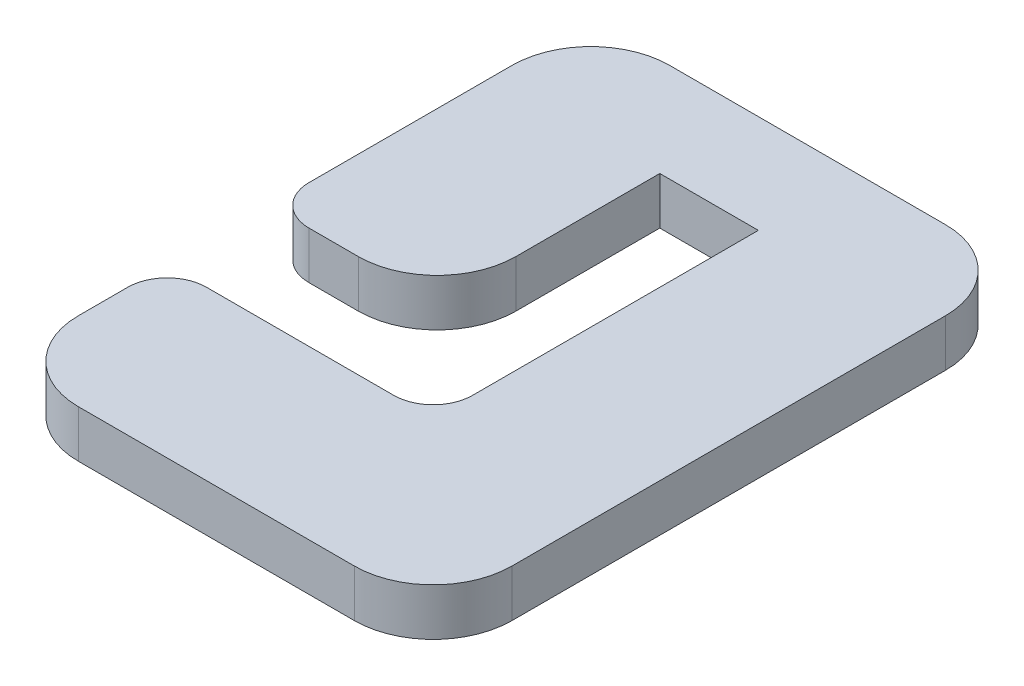
SolidWorks part; units mm, degrees
ref_plane "Front Plane" through (0, 0, 0) normal (0, 0, 1) x (1, 0, 0)
ref_plane "Top Plane" through (0, 0, 0) normal (0, 1, 0) x (1, 0, 0)
ref_plane "Right Plane" through (0, 0, 0) normal (1, 0, 0) x (0, 0, -1)
sketch "Sketch1" plane through (0, 0, 0) normal (0, 1, 0) x (1, 0, 0)
  line L0 (0, -6.5) -> (0, 0) construction
  line L1 (-11, -15) -> (11, -15)
  line L2 (-11, -15) -> (-11, -6.5)
  line L3 (-11, 15) -> (11, 15)
  line L4 (11, -15) -> (11, 15)
  line L5 (-11, -15) -> (-2.5, -3.4091) construction
  line L6 (-11, 15) -> (11, -15) construction
  line L7 (-2.5, 10) -> (2.5, 10)
  line L8 (-2.5, 10) -> (-2.5, -1.3)
  line L9 (-2.5, -6.5) -> (2.5, -6.5)
  line L10 (2.5, 10) -> (2.5, -6.5)
  line L11 (-2.5, -3.4091) -> (0, 0) construction
  line L12 (-2.5, -1.3) -> (-11, -1.3)
  line L13 (-2.5, -3.4091) -> (-2.5, -6.5) construction
  line L14 (-2.5, -6.5) -> (-11, -6.5)
  line L15 (-11, -1.3) -> (-11, -6.5) construction
  line L16 (0, 0) -> (11, 15) construction
  line L17 (-2.5, -1.3) -> (-2.5, -3.4091) construction
  line L18 (-2.5, -3.4091) -> (-2.5, -6.5) construction
  line L19 (-2.5, -1.3) -> (-2.5, -3.4091) construction
  line L20 (-11, -6.5) -> (-11, -1.3) construction
  line L21 (-11, -1.3) -> (-11, 15)
  point P0 (0, 0)
  dimension "D1" = 30
  dimension "D2" = 22
  dimension "D3" = 5
  dimension "D4" = 5
  dimension "D5" = 16.5
  dimension "D6" = 5.2
extrude "Boss-Extrude1" add sketch "Sketch1" along normal blind 2.4
fillet "Fillet1" radius 4 1 edges at (-2.5, 1.2, 1.3)
fillet "Fillet2" radius 4 4 edges at (-11, 1.2, 15) (11, 1.2, 15) (11, 1.2, -15) (-11, 1.2, -15)
fillet "Fillet3" radius 2 3 edges at (-11, 1.2, 6.5) (-11, 1.2, 1.3) (2.5, 1.2, 6.5)
